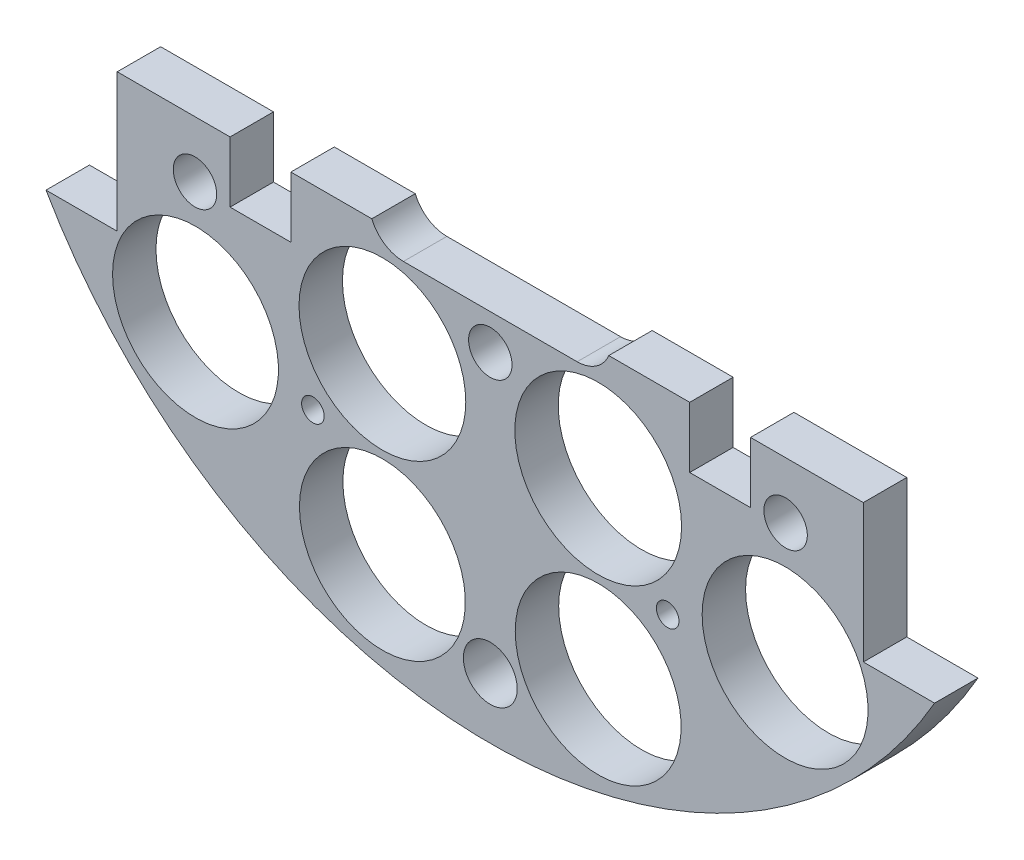
SolidWorks part; units mm, degrees
ref_plane "Front Plane" through (0, 0, 0) normal (0, 0, 1) x (1, 0, 0)
ref_plane "Top Plane" through (0, 0, 0) normal (0, 1, 0) x (1, 0, 0)
ref_plane "Right Plane" through (0, 0, 0) normal (1, 0, 0) x (0, 0, -1)
sketch "Sketch1" plane through (0, 0, 0) normal (0, 0, 1) x (1, 0, 0)
  line L0 (0, 0) -> (-82.1241, 0) construction
  line L1 (0, 0) -> (0, 95.6219) construction
  line L3 (-64.9644, 37.338) -> (-54.5504, 37.338)
  line L5 (-64.9644, -37.338) -> (-54.5504, -37.338)
  line L6 (-54.5504, 37.338) -> (-54.5504, -37.338)
  line L7 (64.9644, -37.338) -> (54.5504, -37.338)
  line L8 (64.9644, 37.338) -> (54.5504, 37.338)
  line L9 (54.5504, 37.338) -> (54.5504, -37.338)
  arc A0 (-64.9644, -37.338) -> (64.9644, -37.338) centre (0, 0) ccw
  circle A1 centre (-46.482, 11.049) radius 1.651
  circle A2 centre (-21.0833, 10.795) radius 1.651
  circle A3 centre (-21.0833, -10.795) radius 1.651
  circle A4 centre (-46.482, -11.049) radius 1.651
  circle A5 centre (46.482, -11.049) radius 1.651
  circle A6 centre (21.0833, -10.795) radius 1.651
  circle A7 centre (21.0833, 10.795) radius 1.651
  circle A8 centre (46.482, 11.049) radius 1.651
  arc A9 (64.9644, 37.338) -> (-64.9644, 37.338) centre (0, 0) ccw
  dimension "D2" = 3.302
  dimension "D3" = 3.302
  dimension "D4" = 25.4
  dimension "D5" = 10.795
  dimension "D10" = 46.482
  dimension "D6" = 74.676
  dimension "D7" = 10.414
  dimension "D8" = 74.93
  dimension "D9" = 74.93
  dimension "D11" = 37.338
extrude "Boss-Extrude2" add sketch "Sketch1" along normal blind 6.35
sketch "Sketch2" plane through (0, 0, 6.35) normal (0, 0, 1) x (1, 0, 0)
  line L0 (0, 68.58) -> (0, 55.88) construction
  line L1 (-9.525, 68.58) -> (9.525, 68.58)
  line L2 (-9.525, 68.58) -> (-9.525, 55.88)
  line L3 (-9.525, 55.88) -> (9.525, 55.88)
  line L4 (9.525, 68.58) -> (9.525, 55.88)
  line L5 (-9.525, 62.23) -> (9.525, 62.23) construction
  arc A0 (64.9644, 37.338) -> (-64.9644, 37.338) centre (0, 0) ccw construction
  circle A1 centre (-21.0833, 10.795) radius 1.651 construction
  circle A2 centre (21.0833, 10.795) radius 1.651 construction
  circle A3 centre (-6.731, 62.23) radius 1.143
  circle A4 centre (6.731, 62.23) radius 1.143
  dimension "D4" = 2.286
  dimension "D5" = 0
  dimension "D6" = 6.731
  dimension "D1" = 19.05
  dimension "D2" = 12.7
  dimension "D3" = 55.88
extrude "Cut-Extrude1" cut sketch "Sketch2" against normal through all contours A3 | A4
sketch "Sketch3" plane through (0, 0, 0) normal (0, 0, -1) x (-1, 0, 0)
  line L0 (0, 0) -> (0, -116.2908) construction
  line L1 (0, 0) -> (-153.8039, 0) construction
  line L2 (0, 0) -> (15.2681, -56.9814) construction
  line L3 (0, 0) -> (15.2302, -26.3795) construction
  circle A0 centre (-15.7776, -58.8828) radius 12.1285
  circle A3 centre (15.7776, -58.8828) radius 12.1285
  circle A4 centre (-43.1052, -43.1052) radius 12.1285
  circle A8 centre (-43.1052, 43.1052) radius 12.1285
  circle A11 centre (43.1052, 43.1052) radius 12.1285
  circle A14 centre (43.1052, -43.1052) radius 12.1285
  circle A33 centre (58.8828, -15.7776) radius 12.1285 [skipped]
  circle A34 centre (58.8828, 15.7776) radius 12.1285 [skipped]
  circle A35 centre (-58.8828, 15.7776) radius 12.1285 [skipped]
  circle A36 centre (-58.8828, -15.7776) radius 12.1285 [skipped]
  circle A37 centre (-15.7776, 58.8828) radius 12.1285 [skipped]
  circle A38 centre (15.7776, 58.8828) radius 12.1285 [skipped]
  point P36 (0, 0)
  point P53 (0, 0)
  point P55 (0, 0)
  dimension "D3" = 0
  dimension "D4" = 15
  dimension "D5" = 24.257
  dimension "D7" = 12
  dimension "D9" = 30
extrude "Cut-Extrude2" cut sketch "Sketch3" against normal through all
sketch "Sketch4" plane through (0, 0, 0) normal (0, 0, -1) x (-1, 0, 0)
  line L1 (-15.7702, 56.3138) -> (12.7925, 56.3138)
  line L2 (-15.7702, 56.3138) -> (-15.7702, 67.9913)
  line L3 (-15.7702, 67.9913) -> (12.7925, 67.9913)
  line L4 (12.7925, 56.3138) -> (12.7925, 67.9913)
extrude "Boss-Extrude3" add sketch "Sketch4" against normal up to surface (6.35 mm away) up to face at (-55.2337, -43.1052, 6.35)
sketch "Sketch5" plane through (0, 0, 0) normal (0, 0, -1) x (-1, 0, 0)
  line L1 (-85.044, -17.145) -> (131.6774, -17.145)
  line L2 (-85.044, -17.145) -> (-85.044, 113.4242)
  line L3 (-85.044, 113.4242) -> (131.6774, 113.4242)
  line L4 (131.6774, -17.145) -> (131.6774, 113.4242)
  circle A0 centre (-21.0833, -10.795) radius 1.651 construction
  dimension "D1" = 6.35
extrude "Cut-Extrude4" cut sketch "Sketch5" against normal through all contours L2 L3 L4 L1
extrude "Cut-Extrude5" cut sketch "Sketch6" against normal through all both and the other way through all
sketch "Sketch6" plane through (31.3134, 132.614, -3.175) normal (0, 0, -1) x (0, 1, 0)
  line L0 (-132.614, -31.3134) -> (-132.614, 57.8454) construction
  line L1 (-132.614, -31.3134) -> (-222.516, -31.3134) construction
  circle A0 centre (-158.014, 14.4066) radius 3.175
  circle A1 centre (-173.254, -31.3134) radius 3.175
  circle A3 centre (-158.014, -77.0334) radius 3.175
  circle A4 centre (-107.214, -77.0334) radius 3.175
  circle A5 centre (-91.974, -31.3134) radius 3.175
  circle A6 centre (-107.214, 14.4066) radius 3.175
extrude "Cut-Extrude7" cut sketch "Sketch8" against normal blind 29.21
sketch "Sketch8" plane through (31.3134, 132.559, 0) normal (0, 0, -1) x (0, 1, 0)
  line L0 (-132.559, -31.3134) -> (6.1626, -31.3134) construction
  line L2 (-132.559, -31.3134) -> (-132.559, -122.6589) construction
  circle A0 centre (-190.979, 2.9766) radius 1.651
  circle A2 centre (-154.784, -31.3134) radius 1.651
  circle A3 centre (-190.979, -65.6034) radius 1.651
  circle A4 centre (-110.334, -31.3134) radius 1.651
  circle A5 centre (-74.139, -65.6034) radius 1.651
  circle A6 centre (-74.139, 2.9766) radius 1.651
sketch "Sketch11" plane through (0, 0, 0) normal (0, 0, -1) x (-1, 0, 0)
  line L0 (-54.5504, -17.145) -> (54.5504, -17.145) construction
  circle A0 centre (0, -66.045) radius 3.937
  point P4 (0, -17.145)
  dimension "D1" = 7.874
  dimension "D2" = 48.9
extrude "Cut-Extrude11" cut sketch "Sketch11" against normal through all
sketch "Sketch12" plane through (0, 0, 0) normal (0, 0, -1) x (-1, 0, 0)
  line L0 (-54.5504, -17.145) -> (54.5504, -17.145) construction
  line L1 (-38.0504, -17.145) -> (-29.1604, -17.145)
  line L2 (-38.0504, -17.145) -> (-38.0504, -26.035)
  line L3 (-38.0504, -26.035) -> (-29.1604, -26.035)
  line L4 (-29.1604, -17.145) -> (-29.1604, -26.035)
  line L5 (-54.5504, -37.338) -> (-54.5504, -17.145) construction
  line L6 (29.1604, -17.145) -> (38.0504, -17.145)
  line L7 (29.1604, -17.145) -> (29.1604, -26.035)
  line L8 (29.1604, -26.035) -> (38.0504, -26.035)
  line L9 (38.0504, -17.145) -> (38.0504, -26.035)
  line L10 (0, -10.2409) -> (0, -88.0539) construction
  dimension "D1" = 16.5
  dimension "D2" = 8.89
  dimension "D3" = 8.89
extrude "Cut-Extrude12" cut sketch "Sketch12" against normal through all
extrude "Cut-Extrude14" cut sketch "Sketch14" against normal through all
sketch "Sketch14" plane through (30.092, 4.0835, -38.1) normal (0, 0, -1) x (-1, 0, 0)
  line L0 (30.092, -4.0835) -> (148.6336, -4.0835) construction
  line L1 (30.092, -4.0835) -> (30.092, 90.452) construction
  circle A0 centre (-13.088, 21.3165) radius 3.175
  circle A1 centre (73.272, 21.3165) radius 3.175
  circle A2 centre (30.092, 21.3165) radius 3.175
  circle A4 centre (73.272, -29.4835) radius 3.175
  circle A5 centre (30.092, -29.4835) radius 3.175
  circle A6 centre (-13.088, -29.4835) radius 3.175
sketch "Sketch15" plane through (0, 0, 0) normal (0, 0, -1) x (-1, 0, 0)
  line L0 (0, 0) -> (0, 42.4042) construction
  line L1 (-12.7, -20.24) -> (-6.06, -20.24)
  line L2 (-6.06, -20.24) -> (12.7, -20.24)
  line L3 (-1.06, -15.24) -> (7.7, -15.24)
  arc A0 (-9.38, -11.5013) -> (-12.7, -20.24) centre (-12.7, -15.24) ccw
  arc A1 (7.7, -15.24) -> (12.7, -20.24) centre (12.7, -15.24) cw
  arc A2 (-1.06, -15.24) -> (-9.38, -11.5013) centre (-6.06, -15.24) ccw
  dimension "D1" = 10
  dimension "D2" = 15.24
  dimension "D3" = 12.7
  dimension "D5" = 6.64
extrude "Cut-Extrude15" cut sketch "Sketch15" against normal blind 21.59
sketch "Sketch16" plane through (0, 0, 0) normal (0, 0, -1) x (-1, 0, 0)
  line L0 (0, 0) -> (0, 27.5884) construction
  circle A0 centre (15.7776, -33.4828) radius 12.192
  circle A2 centre (15.7776, -58.8828) radius 12.1285 construction
  circle A3 centre (-15.7776, -33.4828) radius 12.192
  dimension "D1" = 24.384
  dimension "D2" = 25.4
  dimension "D3" = 0
extrude "Cut-Extrude16" cut sketch "Sketch16" against normal blind 21.59
sketch "Sketch57" plane through (0, 0, 0) normal (0, 0, -1) x (-1, 0, 0)
  line L0 (0, 0) -> (0, -110.6636) construction
  circle A0 centre (-25.9376, -45.6452) radius 1.651
  circle A1 centre (-43.1052, -43.1052) radius 12.1285 construction
  circle A2 centre (-15.7776, -33.4828) radius 12.192 construction
  circle A3 centre (25.9376, -45.6452) radius 1.651
  dimension "D1" = 3.302
  dimension "D2" = 2.54
  dimension "D3" = 10.16
extrude "Cut-Extrude57" cut sketch "Sketch57" against normal blind 58.674
